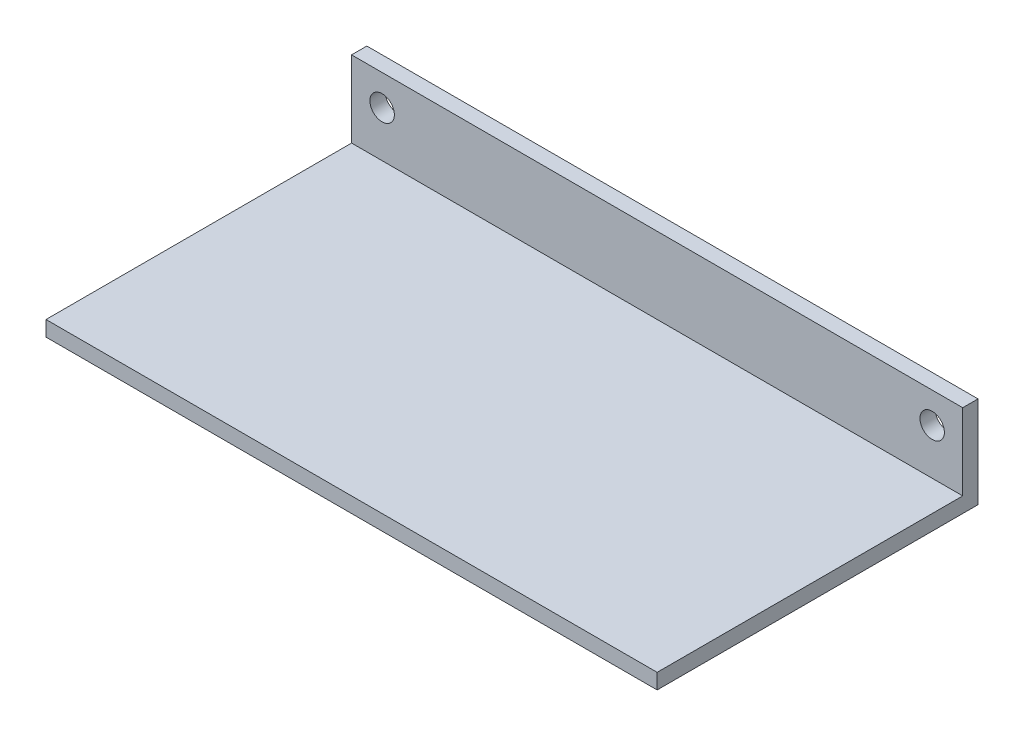
SolidWorks part; units mm, degrees
ref_plane "Front Plane" through (0, 0, 0) normal (0, 0, 1) x (1, 0, 0)
ref_plane "Top Plane" through (0, 0, 0) normal (0, 1, 0) x (1, 0, 0)
ref_plane "Right Plane" through (0, 0, 0) normal (1, 0, 0) x (0, 0, -1)
sketch "Sketch1" plane through (0, 0, 0) normal (0, 1, 0) x (1, 0, 0)
  line L1 (-100, -50) -> (100, -50)
  line L2 (-100, -50) -> (-100, 50)
  line L3 (-100, 50) -> (100, 50)
  line L4 (100, -50) -> (100, 50)
  line L5 (-100, -50) -> (100, 50) construction
  line L6 (-100, 50) -> (100, -50) construction
  point P0 (0, 0)
  dimension "D1" = 100
  dimension "D2" = 200
extrude "Boss-Extrude1" add sketch "Sketch1" along normal blind 5
sketch "Sketch2" plane through (0, 0, 0) normal (0, -1, 0) x (1, 0, 0)
  line L0 (100, 50) -> (100, -50) construction
  line L1 (-100, -50) -> (100, -50)
  line L2 (-100, -50) -> (-100, -55)
  line L3 (-100, -55) -> (100, -55)
  line L4 (100, -50) -> (100, -55)
  dimension "D1" = 5
extrude "Boss-Extrude2" add sketch "Sketch2" against normal blind 30
sketch "Sketch3" plane through (0, 0, -50) normal (0, 0, 1) x (1, 0, 0)
  line L0 (-100, 30) -> (-100, 5) construction
  line L1 (100, 5) -> (-100, 5) construction
  line L2 (100, 30) -> (100, 5) construction
  circle A0 centre (-90, 20) radius 4
  circle A1 centre (90, 20) radius 4
  dimension "D4" = 8
  dimension "D1" = 10
  dimension "D2" = 15
  dimension "D3" = 10
extrude "Cut-Extrude1" cut sketch "Sketch3" against normal blind 40
